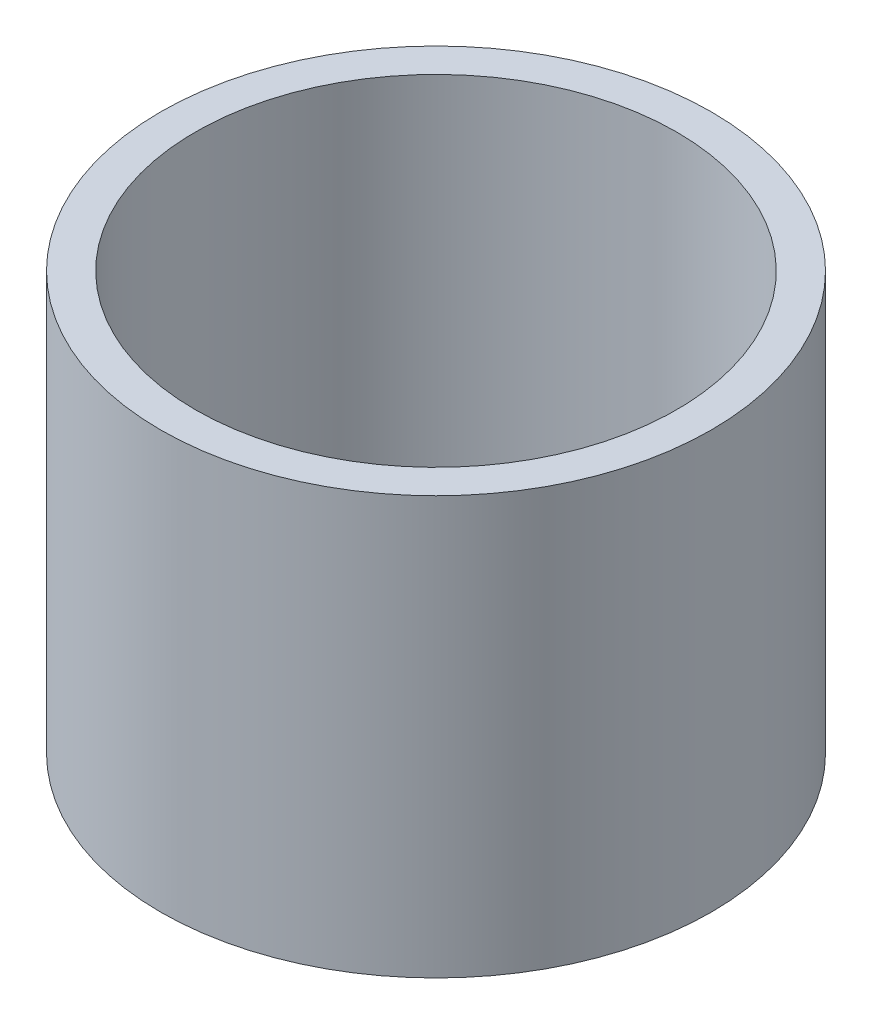
SolidWorks part; units mm, degrees
material "Epoxy, Unfilled"
ref_plane "Front Plane" through (0, 0, 0) normal (0, 0, 1) x (1, 0, 0)
ref_plane "Top Plane" through (0, 0, 0) normal (0, 1, 0) x (1, 0, 0)
ref_plane "Right Plane" through (0, 0, 0) normal (1, 0, 0) x (0, 0, -1)
sketch "Sketch1" plane through (0, 0, 0) normal (0, 1, 0) x (1, 0, 0)
  circle A0 centre (0, 0) radius 50.2539
  circle A1 centre (0, 0) radius 43.9039
extrude "Boss-Extrude1" add sketch "Sketch1" along normal blind 76.2
